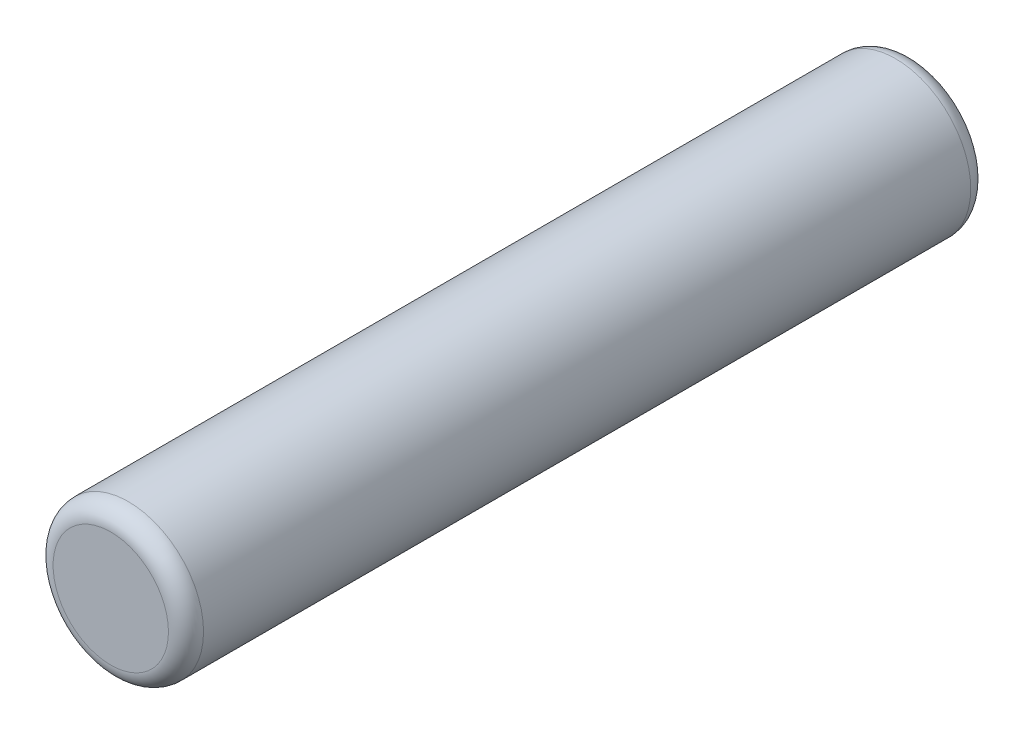
SolidWorks part; units mm, degrees
ref_plane "Front" through (0, 0, 0) normal (0, 0, 1) x (1, 0, 0)
ref_plane "Top" through (0, 0, 0) normal (0, 1, 0) x (1, 0, 0)
ref_plane "Right" through (0, 0, 0) normal (1, 0, 0) x (0, 0, -1)
sketch "Sketch1" plane through (0, 0, 0) normal (0, 0, 1) x (1, 0, 0)
  circle A0 centre (0, 0) radius 1.5
  dimension "D1" = 3
extrude "Boss-Extrude1" add sketch "Sketch1" along normal mid plane 16
fillet "Fillet1" radius 0.35 2 edges at (1.5, 0, -8) (1.5, 0, 8)
